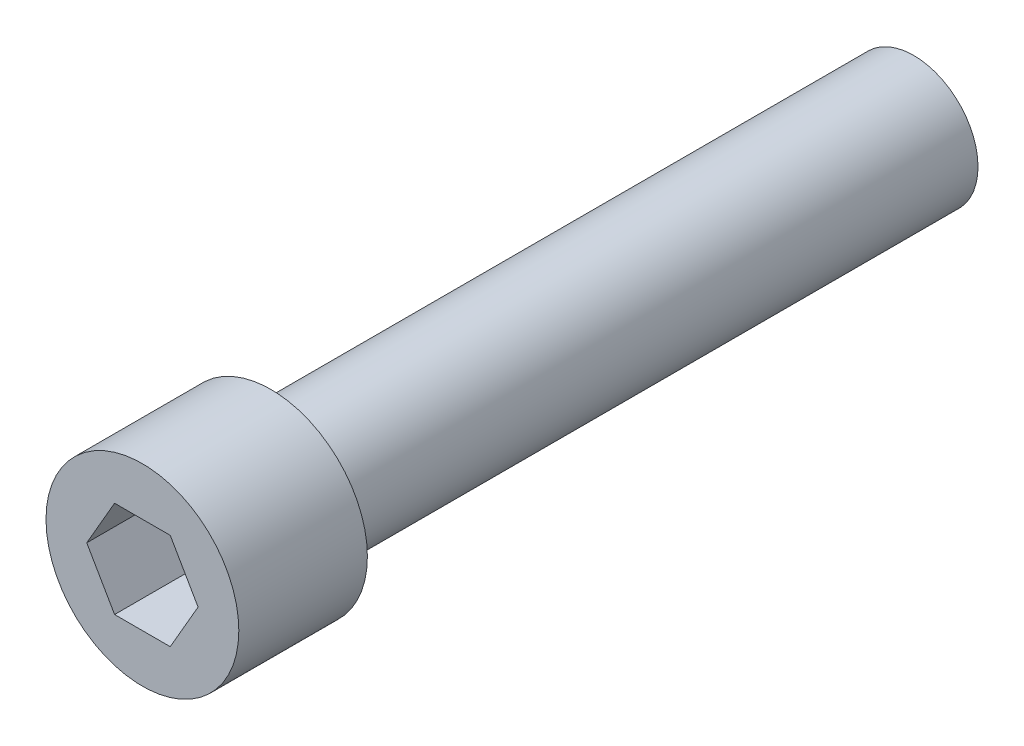
SolidWorks part; units mm, degrees
material "Alloy Steel"
ref_plane "Front Plane" through (0, 0, 0) normal (0, 0, 1) x (1, 0, 0)
ref_plane "Top Plane" through (0, 0, 0) normal (0, 1, 0) x (1, 0, 0)
ref_plane "Right Plane" through (0, 0, 0) normal (1, 0, 0) x (0, 0, -1)
sketch "Sketch1" plane through (0, 0, 0) normal (0, 0, 1) x (1, 0, 0)
  circle A0 centre (0, 0) radius 3.175
  dimension "D1" = 6.35
extrude "Boss-Extrude1" add sketch "Sketch1" along normal blind 31.75
sketch "Sketch2" plane through (0, 0, 31.75) normal (0, 0, 1) x (1, 0, 0)
  circle A0 centre (0, 0) radius 4.7625
  dimension "D1" = 9.525
extrude "Boss-Extrude2" add sketch "Sketch2" along normal blind 6.35
sketch "Sketch3" plane through (0, 0, 38.1) normal (0, 0, 1) x (1, 0, 0)
  line L1 (2.7496, 0) -> (1.3748, 2.3813)
  line L2 (1.3748, 2.3813) -> (-1.3748, 2.3813)
  line L3 (-1.3748, 2.3813) -> (-2.7496, 0)
  line L4 (-2.7496, 0) -> (-1.3748, -2.3813)
  line L5 (-1.3748, -2.3813) -> (1.3748, -2.3813)
  line L6 (1.3748, -2.3813) -> (2.7496, 0)
  circle A0 centre (0, 0) radius 2.3813 construction
  dimension "D1" = 4.7625
extrude "Cut-Extrude1" cut sketch "Sketch3" against normal blind 3.5814
